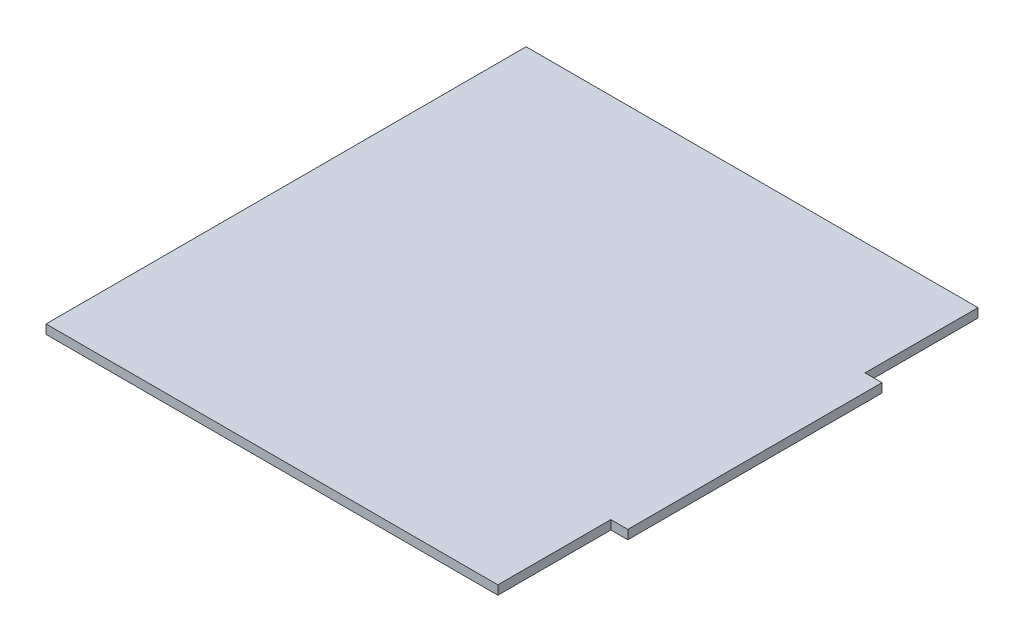
SolidWorks part; units mm, degrees
ref_plane "Front Plane" through (0, 0, 0) normal (0, 0, 1) x (1, 0, 0)
ref_plane "Top Plane" through (0, 0, 0) normal (0, 1, 0) x (1, 0, 0)
ref_plane "Right Plane" through (0, 0, 0) normal (1, 0, 0) x (0, 0, -1)
sketch "Sketch1" plane through (0, 0, 0) normal (0, 1, 0) x (1, 0, 0)
  line L1 (-41.5, -42.5) -> (41.5, -42.5)
  line L2 (-41.5, -42.5) -> (-41.5, 42.5)
  line L3 (-41.5, 42.5) -> (41.5, 42.5)
  line L4 (41.5, -42.5) -> (41.5, 42.5)
  line L5 (-41.5, -42.5) -> (41.5, 42.5) construction
  line L6 (-41.5, 42.5) -> (41.5, -42.5) construction
  point P0 (0, 0)
  dimension "D1" = 83
  dimension "D2" = 85
extrude "Boss-Extrude1" add sketch "Sketch1" along normal blind 1.6
sketch "Sketch2" plane through (0, 1.6, 0) normal (0, 1, 0) x (1, 0, 0)
  line L14 (41.5, 42.5) -> (38.5, 42.5)
  line L15 (41.5, 42.5) -> (41.5, 22.5)
  line L16 (41.5, 22.5) -> (38.5, 22.5)
  line L17 (38.5, 42.5) -> (38.5, 22.5)
  line L18 (41.5, -42.5) -> (38.5, -42.5)
  line L19 (41.5, -42.5) -> (41.5, -22.5)
  line L20 (41.5, -22.5) -> (38.5, -22.5)
  line L21 (38.5, -42.5) -> (38.5, -22.5)
  dimension "D1" = 3
  dimension "D2" = 20
extrude "Cut-Extrude1" cut sketch "Sketch2" against normal blind 10
